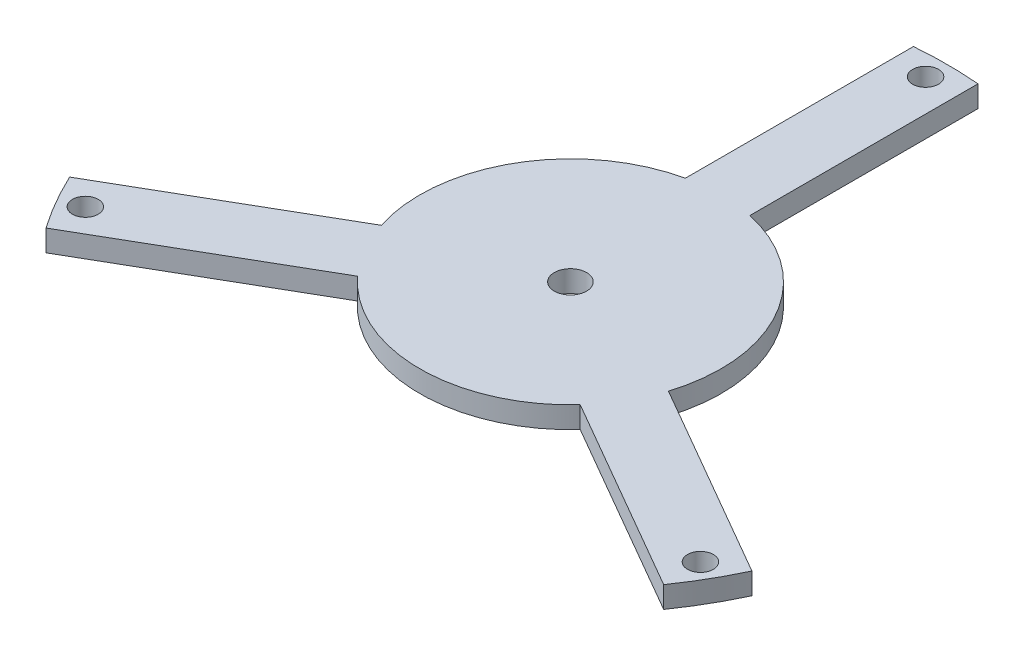
SolidWorks part; units mm, degrees
material "普通碳钢"
ref_plane "前视基准面" through (0, 0, 0) normal (0, 0, 1) x (1, 0, 0)
ref_plane "上视基准面" through (0, 0, 0) normal (0, 1, 0) x (1, 0, 0)
ref_plane "右视基准面" through (0, 0, 0) normal (1, 0, 0) x (0, 0, -1)
sketch "草图1" plane through (0, 0, 0) normal (0, 1, 0) x (1, 0, 0)
  line L0 (-301.5669, 0) -> (327.3767, 0) construction
  line L1 (0, 180.3289) -> (0, -191.1961) construction
  line L2 (0, 0) -> (-277.4906, -160.2093) construction
  line L3 (0, 0) -> (301.6726, -174.1708) construction
  line L4 (-15, 174.356) -> (-15, 68.374)
  line L5 (158.4967, -74.1876) -> (66.7136, -21.1966)
  line L6 (143.4967, -100.1684) -> (51.7136, -47.1774)
  line L7 (-143.4967, -100.1684) -> (-51.7136, -47.1774)
  line L8 (15, 174.356) -> (15, 68.374)
  line L11 (-158.4967, -74.1876) -> (-66.7136, -21.1966)
  circle A0 centre (0, 0) radius 165 construction
  arc A2 (-51.7136, -47.1774) -> (51.7136, -47.1774) centre (0, 0) ccw
  arc A3 (-158.4967, -74.1876) -> (-143.4967, -100.1684) centre (0, 0) ccw
  arc A4 (-15, 68.374) -> (-66.7136, -21.1966) centre (0, 0) ccw
  arc A6 (66.7136, -21.1966) -> (15, 68.374) centre (0, 0) ccw
  arc A7 (15, 174.356) -> (-15, 174.356) centre (0, 0) ccw
  circle A8 centre (0, 165) radius 6
  circle A9 centre (142.8942, -82.5) radius 6
  circle A10 centre (-142.8942, -82.5) radius 6
  arc A11 (143.4967, -100.1684) -> (158.4967, -74.1876) centre (0, 0) ccw
  point P10 (0, 109.6916)
  point P24 (94.9957, -54.8458)
  point P29 (-94.9957, -54.8458)
  point P34 (0, 0)
  point P35 (0, 0)
  dimension "D1" = 330
  dimension "D3" = 140
  dimension "D4" = 350
  dimension "D9" = 12
  dimension "D5" = 120
  dimension "D6" = 120
  dimension "D7" = 30
  dimension "D8" = 3
  dimension "D10" = 3
extrude "凸台-拉伸1" add sketch "草图1" along normal blind 10
sketch "草图2" plane through (0, 10, 0) normal (0, 1, 0) x (1, 0, 0)
  circle A0 centre (0, 0) radius 7.5
  dimension "D1" = 15
extrude "切除-拉伸1" cut sketch "草图2" against normal through all contours A0
